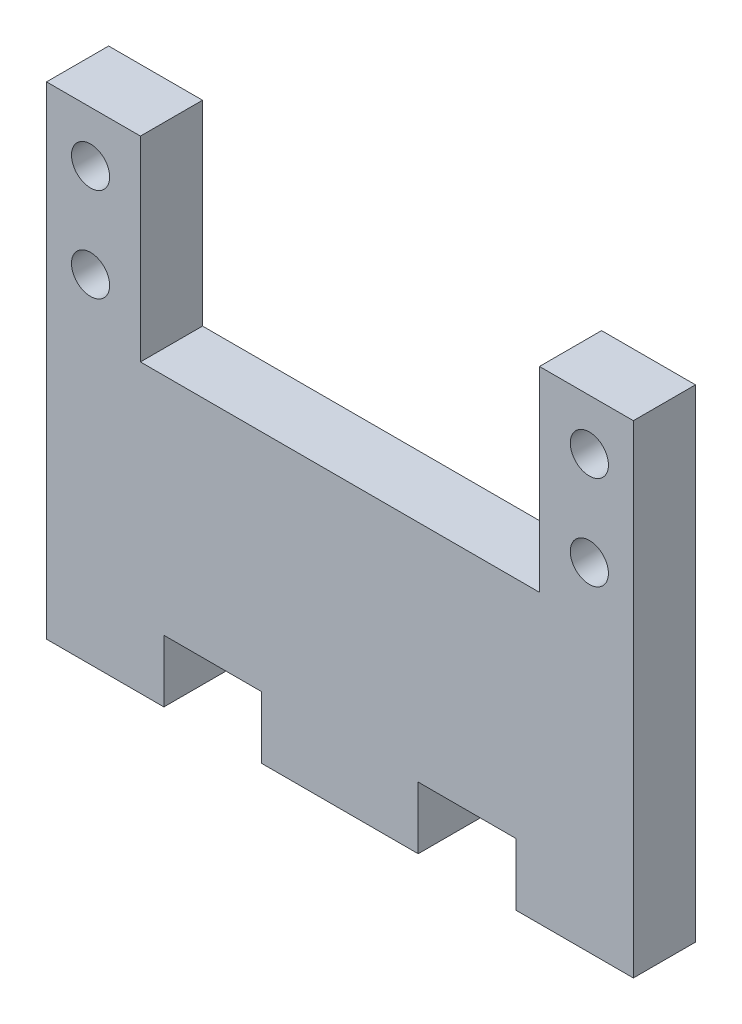
SolidWorks part; units mm, degrees
ref_plane "Front" through (0, 0, 0) normal (0, 0, 1) x (1, 0, 0)
ref_plane "Top" through (0, 0, 0) normal (0, 1, 0) x (1, 0, 0)
ref_plane "Right" through (0, 0, 0) normal (1, 0, 0) x (0, 0, -1)
sketch "Sketch1" plane through (0, 0, 0) normal (0, 0, 1) x (1, 0, 0)
  line L0 (0, 0) -> (0, -21.5) construction
  line L1 (-30, -21.5) -> (30, -21.5) construction
  line L2 (-30, -21.5) -> (-30, 21.5)
  line L3 (-30, 21.5) -> (30, 21.5)
  line L4 (30, -21.5) -> (30, 21.5)
  line L5 (-30, -21.5) -> (30, 21.5) construction
  line L6 (-30, 21.5) -> (30, -21.5) construction
  line L7 (-30, -21.5) -> (-30, -27.85)
  line L8 (-30, -27.85) -> (-18, -27.85)
  line L9 (-18, -27.85) -> (-18, -21.5)
  line L10 (-18, -21.5) -> (-8, -21.5)
  line L11 (-8, -21.5) -> (-8, -27.85)
  line L12 (-8, -27.85) -> (8, -27.85)
  line L13 (-30, -27.85) -> (0, -27.85) construction
  line L14 (30, -21.5) -> (30, -27.85)
  line L15 (30, -27.85) -> (18, -27.85)
  line L16 (18, -27.85) -> (18, -21.5)
  line L17 (18, -21.5) -> (8, -21.5)
  line L18 (8, -21.5) -> (8, -27.85)
  point P0 (0, 0)
  dimension "D1" = 43
  dimension "D2" = 60
  dimension "D3" = 6.35
  dimension "D4" = 10
  dimension "D5" = 12
extrude "Boss-Extrude1" add sketch "Sketch1" along normal blind 6.35
sketch "Sketch2" plane through (0, 0, 6.35) normal (0, 0, 1) x (1, 0, 0)
  line L0 (0, 0) -> (0, 21.5) construction
  line L1 (30, 21.5) -> (-30, 21.5) construction
  line L2 (0, 11.5) -> (-20.4, 11.5) construction
  line L3 (-20.4, 1.5) -> (20.4, 1.5)
  line L4 (-20.4, 1.5) -> (-20.4, 21.5)
  line L5 (-20.4, 21.5) -> (20.4, 21.5)
  line L6 (20.4, 1.5) -> (20.4, 21.5)
  line L7 (-20.4, 1.5) -> (20.4, 21.5) construction
  line L8 (-20.4, 21.5) -> (20.4, 1.5) construction
  circle A0 centre (-25.5, 16.3) radius 1.95
  circle A1 centre (-25.5, 6.7) radius 1.95
  circle A2 centre (25.5, 6.7) radius 1.95
  circle A3 centre (25.5, 16.3) radius 1.95
  point P5 (0, 11.5)
  dimension "D5" = 3.9
  dimension "D1" = 40.8
  dimension "D2" = 20
  dimension "D3" = 4.8
  dimension "D4" = 25.5
extrude "Cut-Extrude1" cut sketch "Sketch2" against normal up to surface (6.35 mm away) up to face at (0, -17.5083, 0)
